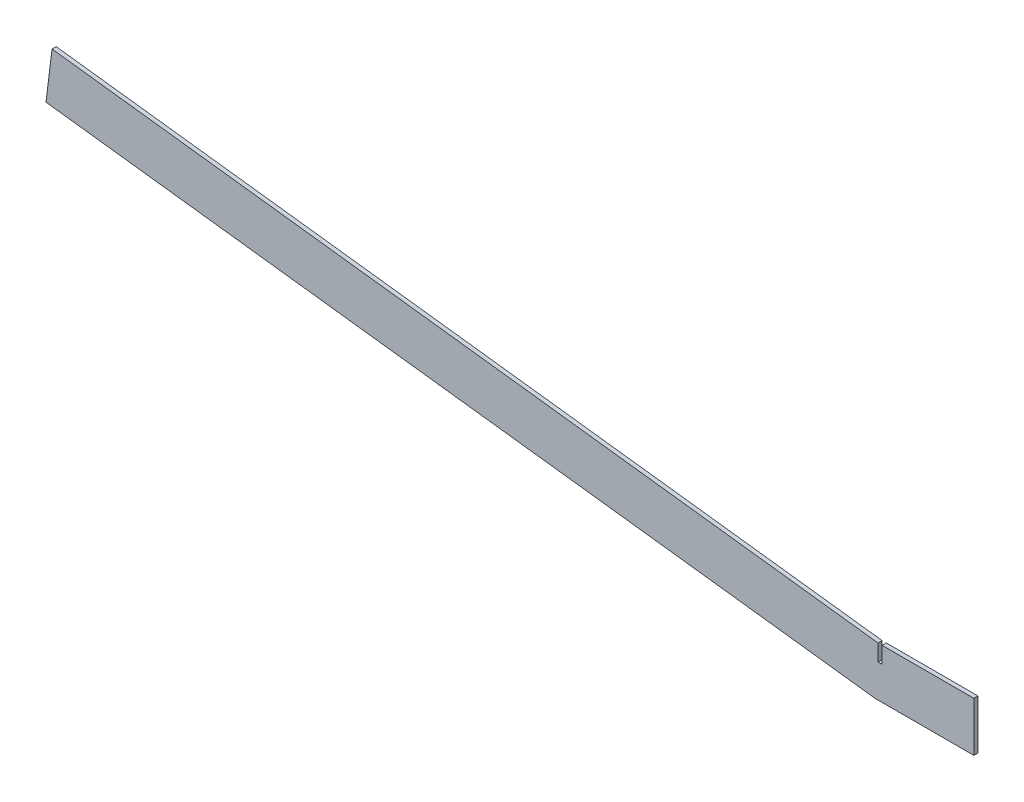
SolidWorks part; units mm, degrees
ref_plane "Front Plane" through (0, 0, 0) normal (0, 0, 1) x (1, 0, 0)
ref_plane "Top Plane" through (0, 0, 0) normal (0, 1, 0) x (1, 0, 0)
ref_plane "Right Plane" through (0, 0, 0) normal (1, 0, 0) x (0, 0, -1)
sketch "Sketch1" plane through (0, 0, 0) normal (0, 0, 1) x (1, 0, 0)
  line L0 (0, 0) -> (-638.481, 78.3956)
  line L1 (-638.481, 78.3956) -> (-633.8378, 116.2116)
  line L2 (-633.8378, 116.2116) -> (2.3303, 38.1)
  line L3 (2.3303, 38.1) -> (76.2, 38.1)
  line L4 (76.2, 38.1) -> (76.2, 0)
  line L5 (76.2, 0) -> (0, 0)
  line L6 (2.3303, 38.1) -> (2.3303, 25.4)
  line L7 (2.3303, 25.4) -> (5.5053, 25.4)
  line L8 (5.5053, 25.4) -> (5.5053, 38.1)
  dimension "D1" = 643.2759
  dimension "D2" = 38.1
  dimension "D3" = 38.1
  dimension "D4" = 3.175
  dimension "D5" = 12.7
  dimension "D6" = 7
  dimension "D7" = 76.2
extrude "Boss-Extrude1" add sketch "Sketch1" along normal mid plane 3.175 contours L8 L7 L6 L2 L1 L0 L5 L4 L3
